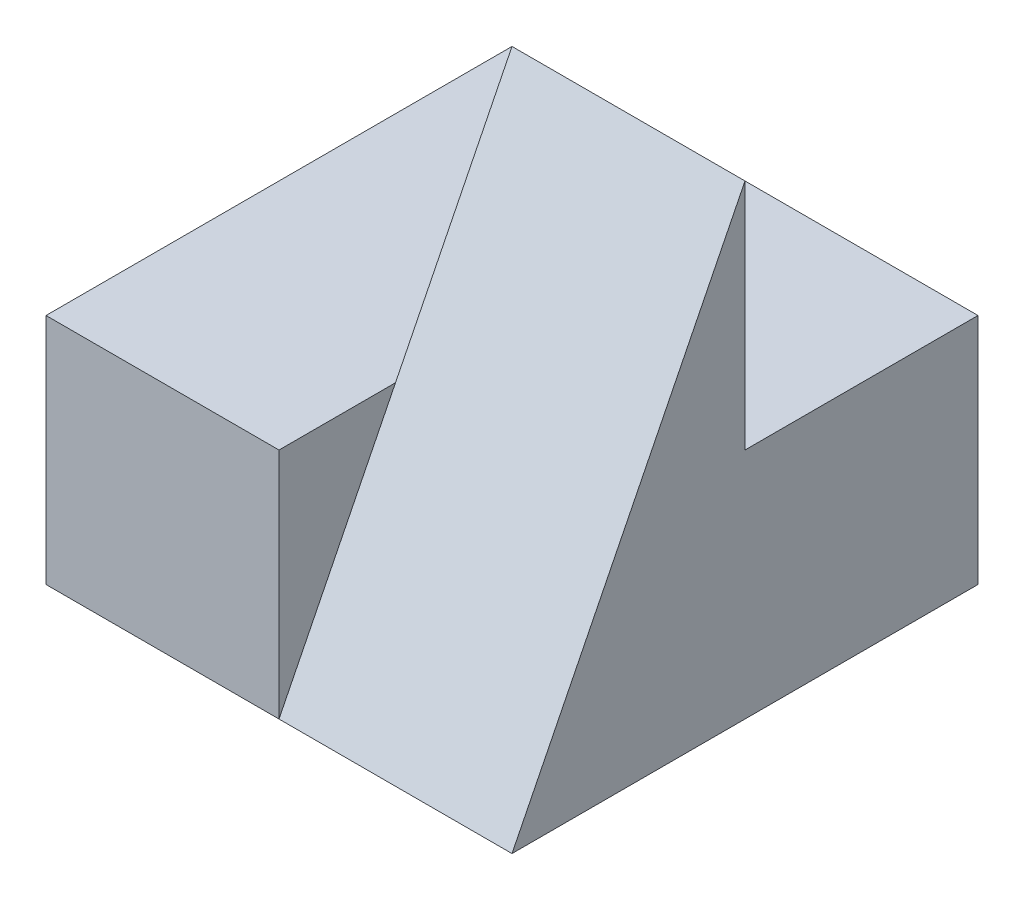
SolidWorks part; units mm, degrees
ref_plane "Front" through (0, 0, 0) normal (0, 0, 1) x (1, 0, 0)
ref_plane "Top" through (0, 0, 0) normal (0, 1, 0) x (1, 0, 0)
ref_plane "Right" through (0, 0, 0) normal (1, 0, 0) x (0, 0, -1)
sketch "Sketch1" plane through (0, 0, 0) normal (0, 1, 0) x (1, 0, 0)
  line L1 (0, 0) -> (4, 0)
  line L2 (0, 0) -> (0, 4)
  line L3 (0, 4) -> (4, 4)
  line L4 (4, 0) -> (4, 4)
  dimension "D1" = 4
  dimension "D2" = 4
extrude "Boss-Extrude1" add sketch "Sketch1" along normal blind 4
sketch "Sketch2" plane through (0, 4, 0) normal (0, 1, 0) x (1, 0, 0)
  line L5 (2, 2) -> (4, 2)
  line L6 (2, 2) -> (2, 0)
  line L7 (2, 0) -> (4, 0)
  line L8 (4, 2) -> (4, 0)
  line L10 (0, 0) -> (4, 0) construction
  line M1 (0, 4) -> (0, 0)
  line M2 (0, 0) -> (4, 0)
  line M3 (4, 0) -> (4, 4)
  line M4 (4, 4) -> (0, 4)
extrude "Cut-Extrude1" cut sketch "Sketch2" against normal blind 2 contours L8 L7 M4 M1 M2 M3
sketch "Sketch3" plane through (4, 0, 0) normal (1, 0, 0) x (0, 0, -1)
  line L0 (2, 4) -> (0, 0)
  line L1 (0, 0) -> (0, 4)
  line L2 (0, 4) -> (2, 4)
extrude "Cut-Extrude2" cut sketch "Sketch3" against normal blind 2
